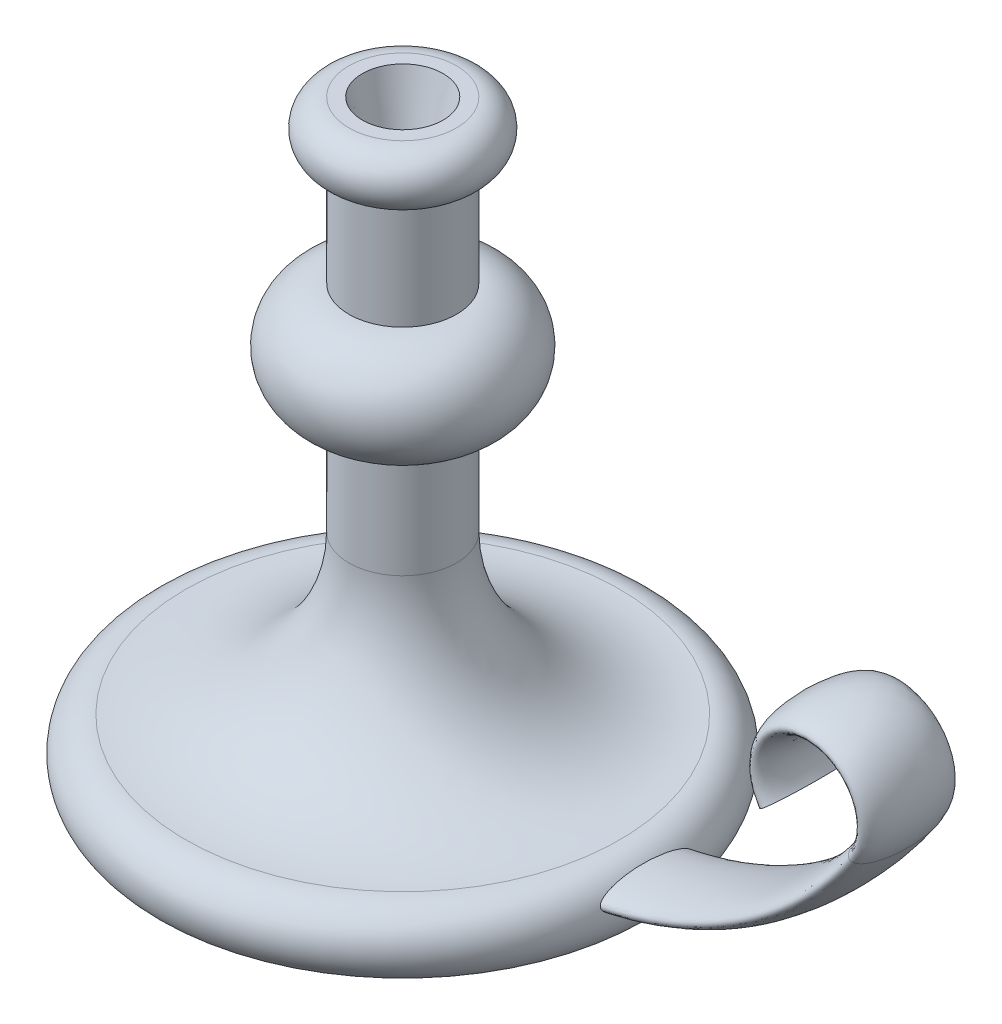
SolidWorks part; units mm, degrees
ref_plane "Front Plane" through (0, 0, 0) normal (0, 0, 1) x (1, 0, 0)
ref_plane "Top Plane" through (0, 0, 0) normal (0, 1, 0) x (1, 0, 0)
ref_plane "Right Plane" through (0, 0, 0) normal (1, 0, 0) x (0, 0, -1)
sketch "Sketch1" plane through (0, 0, 0) normal (0, 0, 1) x (1, 0, 0)
  line L0 (0, 220) -> (0, 0)
  line L1 (0, 0) -> (90, 0)
  line L2 (0, 220) -> (20, 220)
  line L3 (20, 200) -> (20, 160)
  line L4 (20, 120) -> (20, 80)
  arc A0 (20, 220) -> (20, 200) centre (20, 210) cw
  arc A1 (20, 160) -> (20, 120) centre (20, 140) cw
  arc A4 (20, 80) -> (80.6494, 21.208) centre (78.8204, 80) ccw
  arc A5 (80.6494, 21.208) -> (90, 0) centre (81.0381, 8.7141) cw
  dimension "D4" = 10
  dimension "D5" = 20
  dimension "D7" = 58.8204
  dimension "D9" = 12.5
  dimension "D1" = 20
  dimension "D2" = 220
  dimension "D3" = 90
  dimension "D6" = 40
  dimension "D8" = 80
revolve "Revolve1" add sketch "Sketch1" angle 360 about L0
sketch "Sketch2" plane through (0, 0, 0) normal (0, 0, 1) x (1, 0, 0)
  line L0 (0, 10) -> (60, 10)
  line L1 (0, 192.5644) -> (0, 244.8712) construction
  line L2 (0, 160) -> (0, 200) construction
  line L3 (-90, 0) -> (90, 0) construction
  arc A0 (60, 10) -> (183.5921, 75) centre (60, 160) ccw
  arc A1 (183.5921, 75) -> (150.6342, 75) centre (167.1131, 86.3333) ccw
  point P21 (0, 10)
  dimension "D2" = 150
  dimension "D4" = 20
  dimension "D1" = 60
  dimension "D3" = 65
  dimension "D5" = 10
sketch "Sketch3" plane through (0, 0, 0) normal (1, 0, 0) x (0, 0, -1)
  line L0 (0, 116) -> (0, 188) construction
  line L1 (0, 80) -> (0, 120) construction
  ellipse E0 centre (0, 10) end of major axis (17.5, 10) minor radius 5
  dimension "D1" = 10
  dimension "D2" = 35
sweep "Sweep1" add profiles "Sketch3" path "Sketch2"
sketch "Sketch9" plane through (0, 220, 0) normal (0, 1, 0) x (1, 0, 0)
  circle A0 centre (0, 0) radius 15
  dimension "D1" = 30
extrude "Cut-Extrude3" cut sketch "Sketch9" against normal blind 25 draft 15
